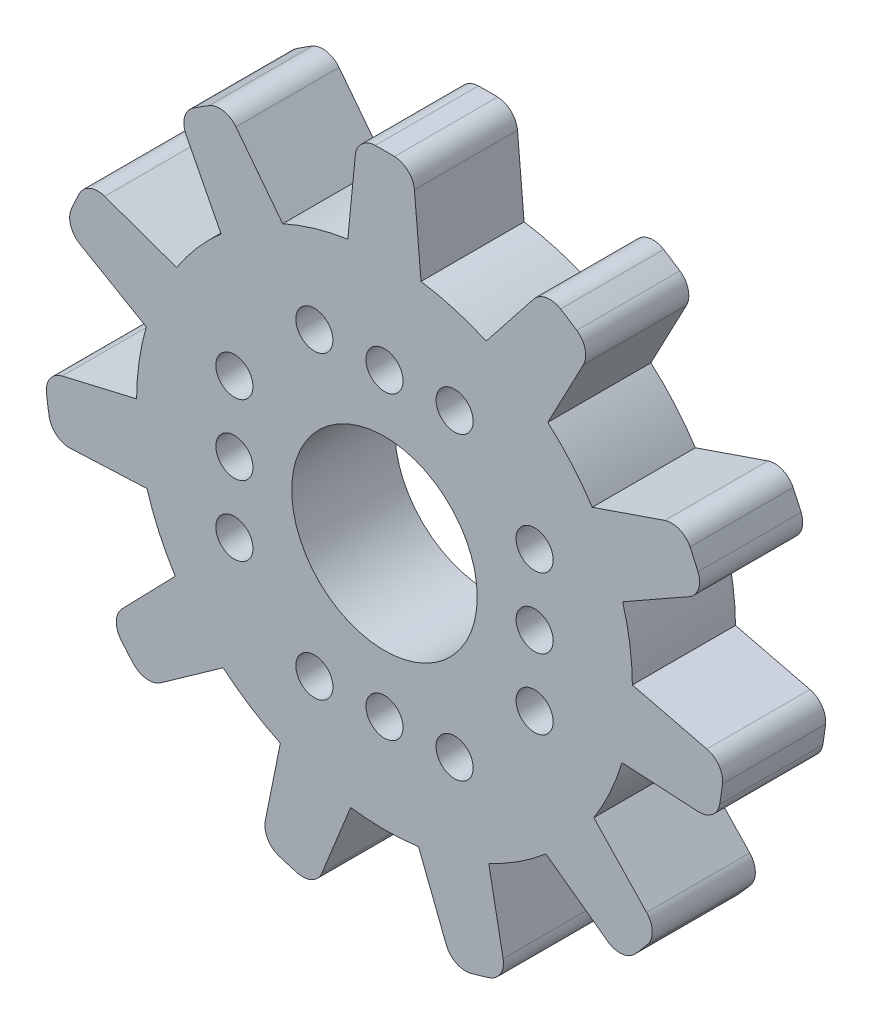
SolidWorks part; units mm, degrees
ref_plane "Plano frontal" through (0, 0, 0) normal (0, 0, 1) x (1, 0, 0)
ref_plane "Plano superior" through (0, 0, 0) normal (0, 1, 0) x (1, 0, 0)
ref_plane "Plano direito" through (0, 0, 0) normal (1, 0, 0) x (0, 0, -1)
sketch "Esboço1" plane through (0, 0, 0) normal (0, 0, 1) x (1, 0, 0)
  line L0 (7.2373, 13.8826) -> (4.9312, 10.964)
  line L1 (9.6438, 12.3222) -> (7.9191, 9.0452)
  line L2 (13.5939, 7.766) -> (10.076, 6.5575)
  line L3 (14.7748, 5.1522) -> (11.5521, 3.3279)
  line L4 (15.6346, -0.8162) -> (12.0217, 0.069)
  line L5 (15.2149, -3.6535) -> (11.5175, -3.446)
  line L6 (12.7114, -9.1393) -> (10.1507, -6.4414)
  line L7 (10.8243, -11.2993) -> (7.8261, -9.1257)
  line L8 (5.7524, -14.5608) -> (5.0568, -10.9067)
  line L9 (2.9971, -15.3576) -> (1.65, -11.9082)
  line L10 (-1.4171, 15.5916) -> (-1.7792, 11.8895)
  line L11 (1.451, 15.5799) -> (1.7718, 11.8907)
  line L12 (-3.0329, -15.3593) -> (-1.6425, -11.9092)
  line L13 (-5.7816, -14.54) -> (-5.05, -10.9098)
  line L14 (-10.8553, -11.2813) -> (-7.8204, -9.1306)
  line L15 (-12.7248, -9.1061) -> (-10.1466, -6.4477)
  line L16 (-15.2312, -3.6216) -> (-11.5153, -3.4532)
  line L17 (-15.6279, -0.781) -> (-12.0218, 0.0615)
  line L18 (-14.7713, 5.1879) -> (-11.5542, 3.3207)
  line L19 (-13.5692, 7.792) -> (-10.0801, 6.5512)
  line L20 (-9.6216, 12.3503) -> (-7.9247, 9.0402)
  line L21 (-7.2025, 13.8912) -> (-4.9381, 10.961)
  arc A0 (-1.7792, 11.8895) -> (-4.9381, 10.961) centre (0, 0) ccw
  circle A1 centre (0, 0) radius 4.5
  arc A2 (0.4841, 16.4929) -> (-0.4491, 16.4939) centre (0, 0) ccw
  arc A3 (1.451, 15.5799) -> (0.4841, 16.4929) centre (0.4548, 15.4933) ccw
  arc A4 (-1.4171, 15.5916) -> (-0.4491, 16.4939) centre (-0.4219, 15.4943) cw
  arc A5 (9.324, 13.613) -> (8.5395, 14.1183) centre (0, 0) ccw
  arc A6 (9.6438, 12.3222) -> (9.324, 13.613) centre (8.7589, 12.7879) ccw
  arc A7 (7.2373, 13.8826) -> (8.5395, 14.1183) centre (8.0219, 13.2627) cw
  arc A8 (15.2036, 6.411) -> (14.8168, 7.2603) centre (0, 0) ccw
  arc A9 (14.7748, 5.1522) -> (15.2036, 6.411) centre (14.2821, 6.0225) ccw
  arc A10 (13.5939, 7.766) -> (14.8168, 7.2603) centre (13.9188, 6.8203) cw
  arc A11 (16.2561, -2.8264) -> (16.3899, -1.9028) centre (0, 0) ccw
  arc A12 (15.2149, -3.6535) -> (16.2561, -2.8264) centre (15.2709, -2.6551) ccw
  arc A13 (15.6346, -0.8162) -> (16.3899, -1.9028) centre (15.3966, -1.7875) cw
  arc A14 (12.1475, -11.1664) -> (12.7593, -10.4618) centre (0, 0) ccw
  arc A15 (10.8243, -11.2993) -> (12.1475, -11.1664) centre (11.4113, -10.4897) ccw
  arc A16 (12.7114, -9.1393) -> (12.7593, -10.4618) centre (11.986, -9.8277) cw
  arc A17 (4.1821, -15.9612) -> (5.0778, -15.6992) centre (0, 0) ccw
  arc A18 (2.9971, -15.3576) -> (4.1821, -15.9612) centre (3.9286, -14.9939) ccw
  arc A19 (5.7524, -14.5608) -> (5.0778, -15.6992) centre (4.77, -14.7478) cw
  arc A20 (-5.1111, -15.6884) -> (-4.216, -15.9523) centre (0, 0) ccw
  arc A21 (-5.7816, -14.54) -> (-5.1111, -15.6884) centre (-4.8013, -14.7376) ccw
  arc A22 (-3.0329, -15.3593) -> (-4.216, -15.9523) centre (-3.9605, -14.9855) cw
  arc A23 (-12.7815, -10.4347) -> (-12.1712, -11.1406) centre (0, 0) ccw
  arc A24 (-12.7248, -9.1061) -> (-12.7815, -10.4347) centre (-12.0069, -9.8023) ccw
  arc A25 (-10.8553, -11.2813) -> (-12.1712, -11.1406) centre (-11.4335, -10.4654) cw
  arc A26 (-16.3939, -1.868) -> (-16.2621, -2.7918) centre (0, 0) ccw
  arc A27 (-15.6279, -0.781) -> (-16.3939, -1.868) centre (-15.4003, -1.7548) ccw
  arc A28 (-15.2312, -3.6216) -> (-16.2621, -2.7918) centre (-15.2765, -2.6226) cw
  arc A29 (-14.8014, 7.2918) -> (-15.1899, 6.4433) centre (0, 0) ccw
  arc A30 (-13.5692, 7.792) -> (-14.8014, 7.2918) centre (-13.9043, 6.8498) ccw
  arc A31 (-14.7713, 5.1879) -> (-15.1899, 6.4433) centre (-14.2693, 6.0528) cw
  arc A32 (-8.5095, 14.1364) -> (-9.2951, 13.6327) centre (0, 0) ccw
  arc A33 (-7.2025, 13.8912) -> (-8.5095, 14.1364) centre (-7.9937, 13.2797) ccw
  arc A34 (-9.6216, 12.3503) -> (-9.2951, 13.6327) centre (-8.7317, 12.8065) cw
  arc A35 (-7.9247, 9.0402) -> (-10.0801, 6.5512) centre (0, 0) ccw
  arc A36 (-11.5542, 3.3207) -> (-12.0218, 0.0615) centre (0, 0) ccw
  arc A37 (-11.5153, -3.4532) -> (-10.1466, -6.4477) centre (0, 0) ccw
  arc A38 (-7.8204, -9.1306) -> (-5.05, -10.9098) centre (0, 0) ccw
  arc A39 (-1.6425, -11.9092) -> (1.65, -11.9082) centre (0, 0) ccw
  arc A40 (5.0568, -10.9067) -> (7.8261, -9.1257) centre (0, 0) ccw
  arc A41 (10.1507, -6.4414) -> (11.5175, -3.446) centre (0, 0) ccw
  arc A42 (12.0217, 0.069) -> (11.5521, 3.3279) centre (0, 0) ccw
  arc A43 (10.076, 6.5575) -> (7.9191, 9.0452) centre (0, 0) ccw
  arc A44 (4.9312, 10.964) -> (1.7718, 11.8907) centre (0, 0) ccw
  point P94 (0, 0)
  dimension "D1" = 1
  dimension "D2" = 11
extrude "Ressalto-extrusão1" add sketch "Esboço1" along normal blind 5
sketch "Esboço3" plane through (0, 0, 0) normal (0, 0, -1) x (-1, 0, 0)
  line L0 (0, 0) -> (0, 7.28) construction
  line L1 (0, 0) -> (7.28, 0) construction
  line L2 (0, 0) -> (0, -7.28) construction
  line L3 (0, 0) -> (-7.28, 0) construction
  circle A0 centre (3.4, 7.28) radius 0.9
  circle A1 centre (0, 7.28) radius 0.9
  circle A2 centre (-3.4, 7.28) radius 0.9
  circle A3 centre (7.28, -3.4) radius 0.9
  circle A4 centre (7.28, 0) radius 0.9
  circle A5 centre (7.28, 3.4) radius 0.9
  circle A6 centre (-3.4, -7.28) radius 0.9
  circle A7 centre (0, -7.28) radius 0.9
  circle A8 centre (3.4, -7.28) radius 0.9
  circle A9 centre (-7.28, 3.4) radius 0.9
  circle A10 centre (-7.28, 0) radius 0.9
  circle A11 centre (-7.28, -3.4) radius 0.9
  point P5 (0, 7.28)
  point P15 (7.28, 0)
  point P22 (0, -7.28)
  point P29 (-7.28, 0)
  point P33 (0, 0)
extrude "Corte-extrusão4" cut sketch "Esboço3" against normal blind 11.8
sketch "Esboço5" plane through (0, 0, 0) normal (0, 0, -1) x (-1, 0, 0)
  line L0 (-7.28, 3.4) -> (-7.28, -3.4) construction
  line L1 (8.18, 3.4) -> (6.38, 3.4)
  line L2 (8.18, 3.4) -> (8.18, -3.4)
  line L3 (8.18, -3.4) -> (6.38, -3.4)
  line L4 (6.38, 3.4) -> (6.38, -3.4)
  line L5 (7.28, -3.4) -> (7.28, 3.4) construction
  line L6 (8.18, 0) -> (6.38, 0) construction
  line L7 (-8.18, 0) -> (-6.38, 0) construction
  line L8 (-8.18, -3.4) -> (-8.18, 3.4)
  line L9 (-8.18, -3.4) -> (-6.38, -3.4)
  line L10 (-6.38, -3.4) -> (-6.38, 3.4)
  line L11 (-8.18, 3.4) -> (-6.38, 3.4)
  circle A0 centre (7.28, -3.4) radius 0.9 construction
  point P0 (7.28, 0)
  point P8 (-7.28, 0)
  point P17 (0, 0)
extrude "Corte-extrusão5" cut sketch "Esboço5" against normal blind 1
